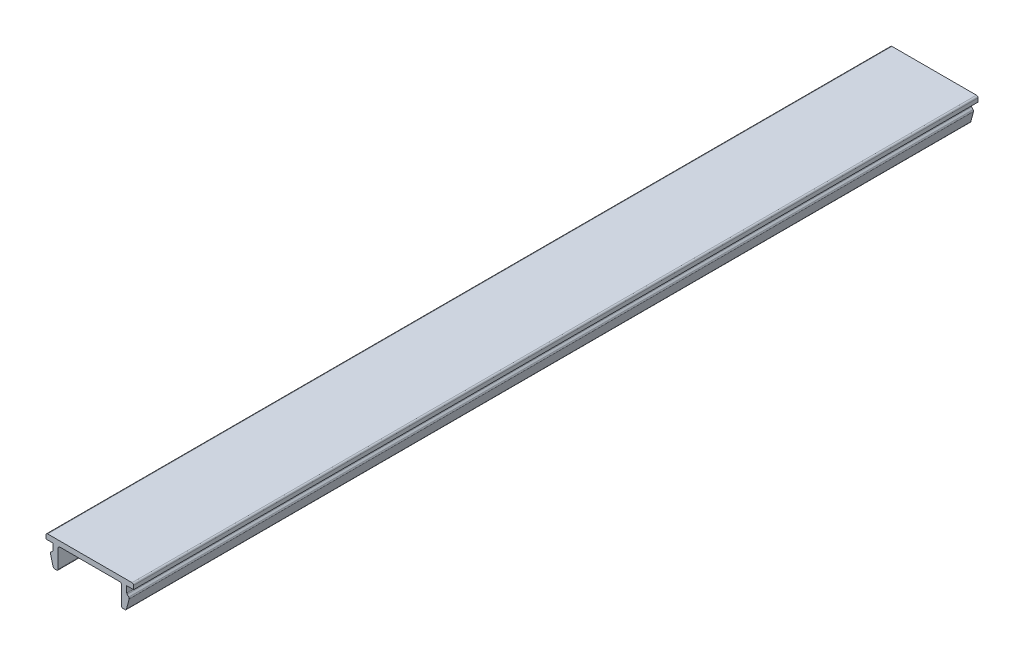
SolidWorks part; units mm, degrees
material "ABS"
ref_plane "Plano frontal" through (0, 0, 0) normal (0, 0, 1) x (1, 0, 0)
ref_plane "Plano superior" through (0, 0, 0) normal (0, 1, 0) x (1, 0, 0)
ref_plane "Plano direito" through (0, 0, 0) normal (1, 0, 0) x (0, 0, -1)
sketch "Sketch1" plane through (0, 0, 0) normal (0, 0, 1) x (1, 0, 0)
  line L0 (-8.3, 1) -> (8.3, 1)
  line L1 (-8.3, 0) -> (-7, 0)
  line L2 (-8.3, 1) -> (-8.3, 0)
  line L3 (8.3, 1) -> (8.3, 0)
  line L4 (-7, 0) -> (-7, -1.3)
  line L5 (-7, -1.3) -> (-7.5, -1.8)
  line L6 (-7.5, -1.8) -> (-6.8837, -4.1)
  line L7 (-6, 0) -> (-6, -4.1)
  line L8 (-6, -4.1) -> (-6.8837, -4.1)
  line L9 (0, 0) -> (0, -1.7195) construction
  line L10 (6, -4.1) -> (6.8837, -4.1)
  line L11 (6, 0) -> (6, -4.1)
  line L12 (7.5, -1.8) -> (6.8837, -4.1)
  line L13 (7, -1.3) -> (7.5, -1.8)
  line L14 (7, 0) -> (7, -1.3)
  line L15 (7, 0) -> (8.3, 0)
  line L16 (-8.3, 0) -> (8.3, 0) construction
  line L17 (-6, 0) -> (6, 0)
  point P21 (0, 1)
  dimension "D1" = 16.6
  dimension "D3" = 1.3
  dimension "D4" = 1.3
  dimension "D5" = 135
  dimension "D6" = 120
  dimension "D7" = 4.1
  dimension "D8" = 0.5
  dimension "D9" = 1
  dimension "D2" = 1
extrude "Boss-Extrude1" add sketch "Sketch1" along normal blind 160
fillet "Fillet1" radius 0.3 12 edges at (8.3, 1, 80) (7, -1.3, 80) (7.5, -1.8, 80) (6.8837, -4.1, 80) (6, -4.1, 80) (6, 0, 80) (-6, 0, 80) (-6, -4.1, 80) (-6.8837, -4.1, 80) (-7.5, -1.8, 80) (-7, -1.3, 80) (-8.3, 1, 80)
